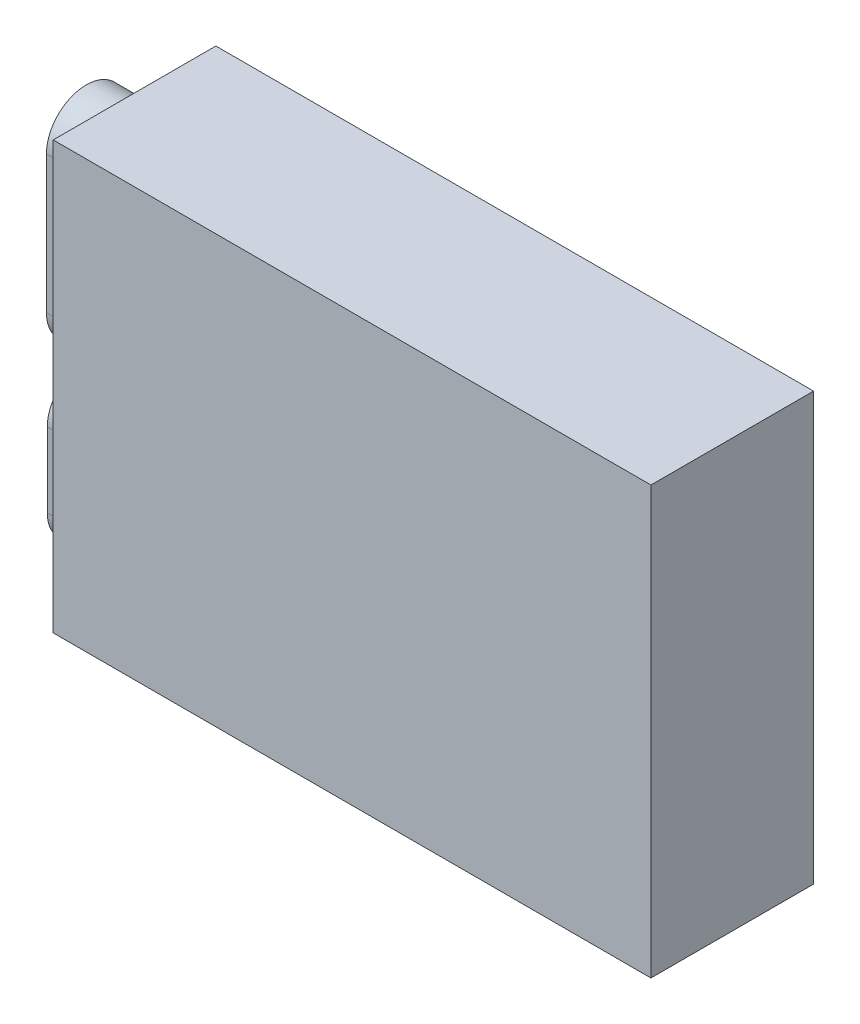
SolidWorks part; units mm, degrees
ref_plane "Front Plane" through (0, 0, 0) normal (0, 0, 1) x (1, 0, 0)
ref_plane "Top Plane" through (0, 0, 0) normal (0, 1, 0) x (1, 0, 0)
ref_plane "Right Plane" through (0, 0, 0) normal (1, 0, 0) x (0, 0, -1)
sketch "Sketch1" plane through (0, 0, 0) normal (0, 0, 1) x (1, 0, 0)
  line L1 (73.5, -52.5) -> (-73.5, -52.5)
  line L2 (73.5, -52.5) -> (73.5, 52.5)
  line L3 (73.5, 52.5) -> (-73.5, 52.5)
  line L4 (-73.5, -52.5) -> (-73.5, 52.5)
  line L5 (73.5, -52.5) -> (-73.5, 52.5) construction
  line L6 (73.5, 52.5) -> (-73.5, -52.5) construction
  point P0 (0, 0)
extrude "Boss-Extrude4" add sketch "Sketch1" along normal blind 40
sketch "Sketch6" plane through (-73.5, 0, 0) normal (-1, 0, 0) x (0, 0, 1)
  line L0 (19.1655, 3.8595) -> (19.1655, 37.6562) construction
  line L1 (9.3603, 3.8595) -> (9.3603, 37.6562)
  line L2 (28.9707, 3.8595) -> (28.9707, 37.6562)
  arc A0 (9.3603, 3.8595) -> (28.9707, 3.8595) centre (19.1655, 3.8595) ccw
  arc A1 (28.9707, 37.6562) -> (9.3603, 37.6562) centre (19.1655, 37.6562) ccw
  point P2 (19.1655, 20.7578)
extrude "Boss-Extrude5" add sketch "Sketch6" along normal blind 12.7
sketch "Sketch7" plane through (-86.2, 0, 0) normal (-1, 0, 0) x (0, 0, 1)
  line L0 (19.5699, 3.8595) -> (19.1655, 37.6562) construction
  line L1 (12.1544, 3.7708) -> (11.75, 37.5674)
  line L2 (26.9854, 3.9482) -> (26.581, 37.7449)
  arc A0 (12.1544, 3.7708) -> (26.9854, 3.9482) centre (19.5699, 3.8595) ccw
  arc A1 (26.581, 37.7449) -> (11.75, 37.5674) centre (19.1655, 37.6562) ccw
  point P2 (19.3677, 20.7578)
extrude "Cut-Extrude3" cut sketch "Sketch7" against normal blind 10.16
sketch "Sketch8" plane through (-73.5, 0, 0) normal (-1, 0, 0) x (0, 0, 1)
  line L0 (19.5828, -38.9079) -> (19.5828, -20.5492) construction
  line L1 (10.4034, -38.9079) -> (10.4034, -20.5492)
  line L2 (28.7621, -38.9079) -> (28.7621, -20.5492)
  arc A0 (10.4034, -38.9079) -> (28.7621, -38.9079) centre (19.5828, -38.9079) ccw
  arc A1 (28.7621, -20.5492) -> (10.4034, -20.5492) centre (19.5828, -20.5492) ccw
  point P2 (19.5828, -29.7286)
extrude "Boss-Extrude6" add sketch "Sketch8" along normal blind 12.7
sketch "Sketch9" plane through (-86.2, 0, 0) normal (-1, 0, 0) x (0, 0, 1)
  line L0 (19.6345, -38.9079) -> (19.5828, -20.5492) construction
  line L1 (12.3883, -38.9283) -> (12.3366, -20.5696)
  line L2 (26.8807, -38.8875) -> (26.829, -20.5288)
  arc A0 (12.3883, -38.9283) -> (26.8807, -38.8875) centre (19.6345, -38.9079) ccw
  arc A1 (26.829, -20.5288) -> (12.3366, -20.5696) centre (19.5828, -20.5492) ccw
  point P2 (19.6086, -29.7286)
extrude "Cut-Extrude4" cut sketch "Sketch9" against normal blind 10.16
